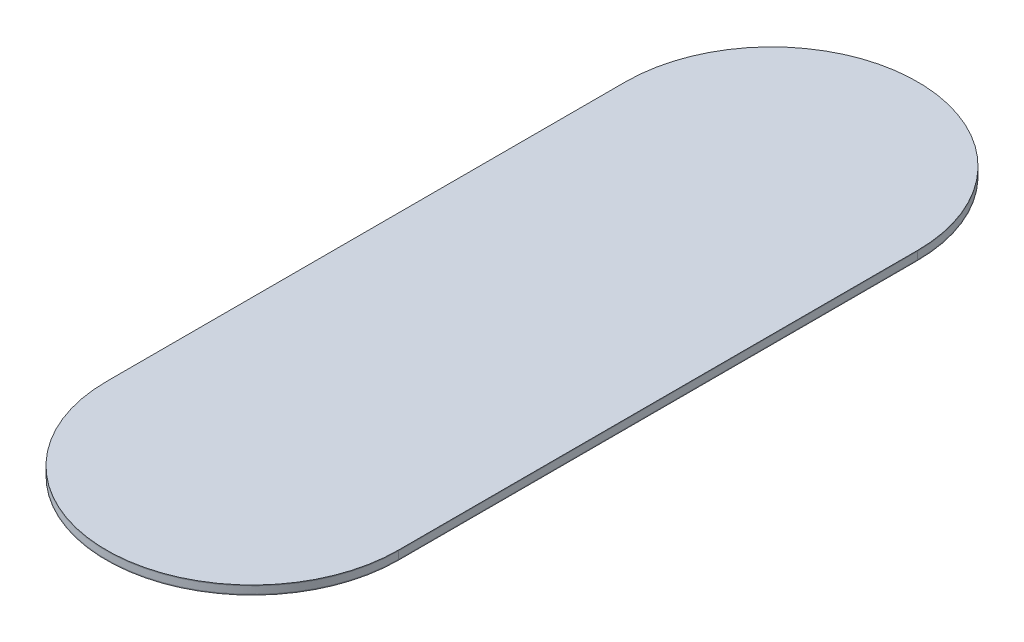
SolidWorks part; units mm, degrees
ref_plane "Front Plane" through (0, 0, 0) normal (0, 0, 1) x (1, 0, 0)
ref_plane "Top Plane" through (0, 0, 0) normal (0, 1, 0) x (1, 0, 0)
ref_plane "Right Plane" through (0, 0, 0) normal (1, 0, 0) x (0, 0, -1)
sketch "Sketch1" plane through (0, 0, 0) normal (0, 1, 0) x (1, 0, 0)
  line L0 (0, -88.9) -> (0, 88.9) construction
  line L2 (50, 88.9) -> (50, -88.9)
  line L3 (0, 0) -> (-26.323, 0) construction
  line L14 (-50, 88.9) -> (-50, -88.9)
  arc A0 (50, 88.9) -> (-50, 88.9) centre (0, 88.9) ccw
  arc A1 (-50, -88.9) -> (50, -88.9) centre (0, -88.9) ccw
  point P8 (0, 0)
  point P13 (-89.4761, 0)
  point P18 (-35.323, 0)
  dimension "D2" = 100
  dimension "D1" = 177.8
extrude "Boss-Extrude1" add sketch "Sketch1" along normal blind 0.25
sketch "Sketch5" plane through (0, 0.25, 0) normal (0, 1, 0) x (1, 0, 0)
  line L2 (-50, 88.9) -> (-50, -88.9)
  line L3 (50, -88.9) -> (50, 88.9)
  line L4 (-50, 88.9) -> (-50, -88.9)
  line L5 (50, -88.9) -> (50, 88.9)
  arc A2 (50, 88.9) -> (-50, 88.9) centre (0, 88.9) ccw
  arc A3 (-50, -88.9) -> (50, -88.9) centre (0, -88.9) ccw
  arc A4 (50, 88.9) -> (-50, 88.9) centre (0, 88.9) ccw
  arc A5 (-50, -88.9) -> (50, -88.9) centre (0, -88.9) ccw
  dimension "D1" = 0
extrude "Boss-Extrude6" add sketch "Sketch5" along normal blind 2.5 separate body
sketch "Sketch6" plane through (0, 2.75, 0) normal (0, 1, 0) x (1, 0, 0)
  line L2 (-50, 88.9) -> (-50, -88.9)
  line L3 (50, -88.9) -> (50, 88.9)
  line L4 (-50, 88.9) -> (-50, -88.9)
  line L5 (50, -88.9) -> (50, 88.9)
  arc A2 (50, 88.9) -> (-50, 88.9) centre (0, 88.9) ccw
  arc A3 (-50, -88.9) -> (50, -88.9) centre (0, -88.9) ccw
  arc A4 (50, 88.9) -> (-50, 88.9) centre (0, 88.9) ccw
  arc A5 (-50, -88.9) -> (50, -88.9) centre (0, -88.9) ccw
  dimension "D1" = 0
extrude "Boss-Extrude7" add sketch "Sketch6" along normal blind 0.25 separate body
